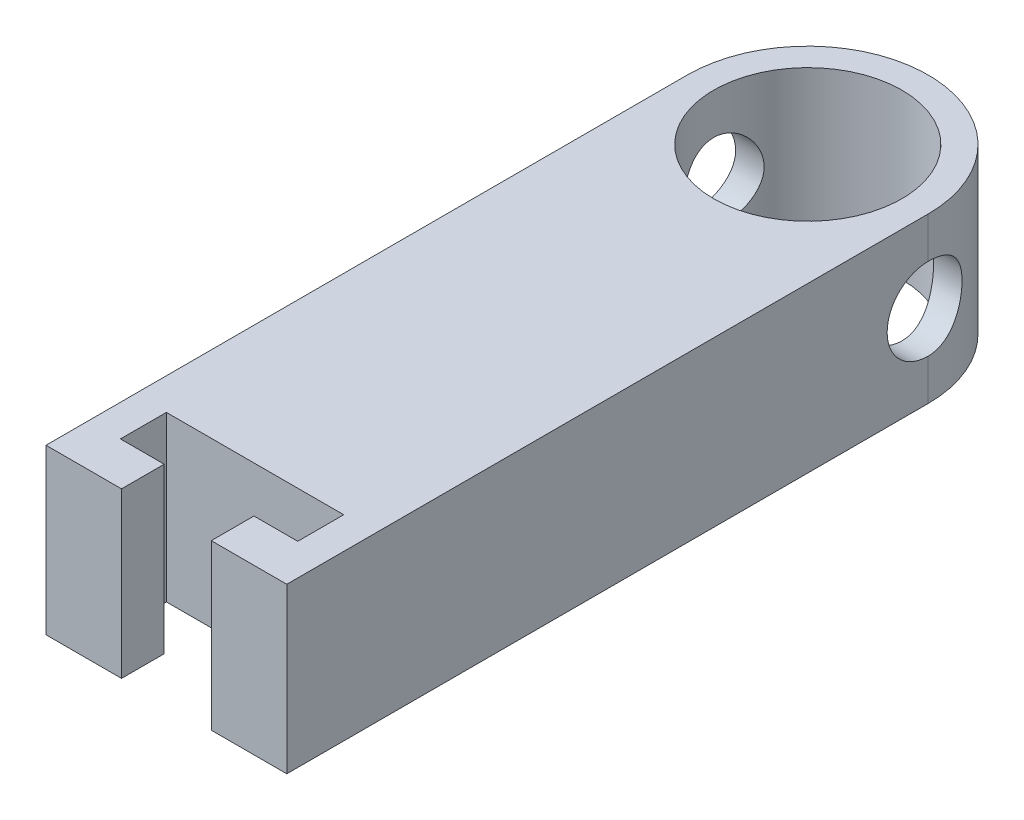
SolidWorks part; units mm, degrees
ref_plane "Front Plane" through (0, 0, 0) normal (0, 0, 1) x (1, 0, 0)
ref_plane "Top Plane" through (0, 0, 0) normal (0, 1, 0) x (1, 0, 0)
ref_plane "Right Plane" through (0, 0, 0) normal (1, 0, 0) x (0, 0, -1)
sketch "Sketch2" plane through (0, 0, 0) normal (0, 0, 1) x (1, 0, 0)
  line L0 (-4.699, 24.13) -> (4.699, 24.13)
  line L1 (-10.16, 20.32) -> (10.16, 20.32)
  line L2 (-10.16, 20.32) -> (-10.16, 27.94)
  line L3 (-10.16, 27.94) -> (10.16, 27.94)
  line L4 (10.16, 20.32) -> (10.16, 27.94)
  line L5 (-10.16, 20.32) -> (10.16, 27.94) construction
  line L6 (-10.16, 27.94) -> (10.16, 20.32) construction
  line L7 (55, 0) -> (-55, 0) construction
  line L8 (-10.16, -27.94) -> (10.16, -20.32) construction
  line L9 (-10.16, -20.32) -> (10.16, -27.94) construction
  line L10 (10.16, -20.32) -> (10.16, -27.94)
  line L11 (-10.16, -27.94) -> (10.16, -27.94)
  line L12 (-10.16, -20.32) -> (-10.16, -27.94)
  line L13 (-10.16, -20.32) -> (10.16, -20.32)
  line L14 (-4.699, -24.13) -> (4.699, -24.13)
  circle A0 centre (4.699, 24.13) radius 1.905
  circle A1 centre (-4.699, 24.13) radius 1.905
  circle A2 centre (-4.699, -24.13) radius 1.905
  circle A3 centre (4.699, -24.13) radius 1.905
  point P0 (0, 24.13)
  point P10 (0, 24.13)
  point P23 (0, -24.13)
  dimension "D5" = 3.81
  dimension "D1" = 20.32
  dimension "D2" = 7.62
  dimension "D3" = 20.32
  dimension "D4" = 9.398
extrude "Boss-Extrude1" add sketch "Sketch2" along normal blind 12.7
sketch "Sketch4" plane through (0, 0, 12.7) normal (0, 0, 1) x (1, 0, 0)
  line L0 (-10.16, -27.94) -> (10.16, -27.94) construction
  line L1 (-10.16, 27.94) -> (-17.78, 27.94)
  line L2 (-10.16, 27.94) -> (-10.16, -27.94)
  line L3 (-10.16, -27.94) -> (-17.78, -27.94)
  line L4 (-17.78, 27.94) -> (-17.78, -27.94)
  dimension "D1" = 7.62
extrude "Boss-Extrude2" add sketch "Sketch4" against normal blind 28.702
sketch "Sketch5" plane through (0, 0, -16.002) normal (0, 0, -1) x (-1, 0, 0)
  line L1 (17.78, 27.94) -> (-10.16, 27.94)
  line L2 (17.78, 27.94) -> (17.78, -27.94)
  line L3 (17.78, -27.94) -> (-10.16, -27.94)
  line L4 (-10.16, 27.94) -> (-10.16, -27.94)
extrude "Boss-Extrude3" add sketch "Sketch5" along normal blind 7.62
sketch "Sketch6" plane through (0, 27.94, 0) normal (0, 1, 0) x (1, 0, 0)
  line L0 (-17.78, 23.622) -> (10.16, 23.622) construction
  line L1 (4.9004, 23.622) -> (10.16, 23.622)
  line L2 (-17.78, 34.544) -> (-17.78, 23.622)
  line L3 (10.16, 34.544) -> (10.16, 23.622)
  line L4 (-17.78, 23.622) -> (-12.5204, 23.622)
  circle A0 centre (-3.81, 34.544) radius 10.922
  arc A1 (-12.5204, 23.622) -> (4.9004, 23.622) centre (-3.81, 34.544) ccw
  circle A2 centre (-3.81, 34.544) radius 13.97 construction
  arc A3 (10.16, 34.544) -> (-17.78, 34.544) centre (-3.81, 34.544) ccw
  point P4 (-3.81, 23.622)
  dimension "D1" = 21.844
  dimension "D2" = 3.048
extrude "Boss-Extrude6" add sketch "Sketch6" against normal up to surface (55.88 mm away) up to face at (-1.905, -27.94, -6.731)
sketch "Sketch7" plane through (10.16, 0, 0) normal (1, 0, 0) x (0, 0, -1)
  line L1 (48.514, 27.94) -> (34.544, 27.94) construction
  circle A0 centre (34.544, 18.415) radius 4.7625
  point P4 (0, 0)
  point P5 (0, 0)
  dimension "D1" = 9.525
  dimension "D2" = 9.525
extrude "Cut-Extrude1" cut sketch "Sketch7" against normal through all both and the other way through all
sketch "Sketch8" plane through (0, 0, -16.002) normal (0, 0, 1) x (1, 0, 0)
  line L1 (-17.78, 27.94) -> (10.16, 27.94)
  line L2 (-17.78, 27.94) -> (-17.78, -27.94)
  line L3 (-17.78, -27.94) -> (10.16, -27.94)
  line L4 (10.16, 27.94) -> (10.16, -27.94)
extrude "Cut-Extrude2" cut sketch "Sketch8" along normal through all
sketch "Sketch9" plane through (0, -27.94, 0) normal (0, -1, 0) x (-1, 0, 0)
  line L3 (-10.16, 16.002) -> (17.78, 16.002)
  line L4 (17.78, 16.002) -> (17.78, 34.544)
  line L5 (-10.16, 34.544) -> (-10.16, 16.002)
  line L6 (-10.16, 16.002) -> (17.78, 16.002)
  line L7 (17.78, 16.002) -> (17.78, 34.544)
  line L8 (-10.16, 34.544) -> (-10.16, 16.002)
  arc A1 (17.78, 34.544) -> (-10.16, 34.544) centre (3.81, 34.544) ccw
  arc A2 (17.78, 34.544) -> (-10.16, 34.544) centre (3.81, 34.544) ccw
  dimension "D1" = 0
extrude "Cut-Extrude3" cut sketch "Sketch9" against normal blind 36.83
sketch "Sketch10" plane through (0, 27.94, 0) normal (0, 1, 0) x (1, 0, 0)
  line L0 (-9.017, -34.671) -> (-9.017, -40.005)
  line L5 (-17.78, 16.002) -> (10.16, 16.002) construction
  line L6 (-13.97, -29.718) -> (6.35, -29.718)
  line L7 (-13.97, -29.718) -> (-13.97, -34.798)
  line L8 (-13.97, -34.798) -> (6.35, -34.798)
  line L9 (6.35, -29.718) -> (6.35, -34.798)
  line L10 (-8.89, -34.798) -> (1.27, -34.798)
  line L11 (-8.89, -34.798) -> (-8.89, -39.878)
  line L12 (-8.89, -39.878) -> (1.27, -39.878)
  line L13 (1.27, -34.798) -> (1.27, -39.878)
  line L14 (10.16, 34.544) -> (10.16, 16.002) construction
  line L15 (-17.78, 16.002) -> (10.16, 16.002)
  line L16 (-17.78, 16.002) -> (-17.78, -39.878)
  line L17 (-17.78, -39.878) -> (10.16, -39.878)
  line L18 (10.16, 16.002) -> (10.16, -39.878)
  line L19 (-3.81, 23.622) -> (10.16, 23.622)
  line L20 (-9.017, -40.005) -> (1.397, -40.005)
  line L21 (1.397, -34.671) -> (1.397, -40.005)
  line L22 (-9.017, -34.671) -> (1.397, -34.671)
  line L23 (-14.097, -29.591) -> (-14.097, -34.925)
  line L24 (-14.097, -34.925) -> (6.477, -34.925)
  line L25 (6.477, -29.591) -> (6.477, -34.925)
  line L26 (-14.097, -29.591) -> (6.477, -29.591)
  circle A0 centre (-3.81, 34.544) radius 10.922 construction
  circle A1 centre (-3.81, 34.544) radius 10.922
  point P4 (-3.81, -29.718)
  point P5 (-3.81, 16.002)
  point P13 (-3.81, -39.878)
  point P25 (-3.81, -8.6885)
  line M17 (-17.78, 16.002) -> (10.16, 16.002)
  dimension "D4" = 53.34
  dimension "D1" = 20.32
  dimension "D2" = 5.08
  dimension "D3" = 10.16
  dimension "D5" = 5.08
  dimension "D6" = 0.127
extrude "Boss-Extrude7" add sketch "Sketch10" against normal up to surface (19.05 mm away) contours L23 L26 L25 L24 L21 L17 L18 L16 L0 M17 up to face at (-3.81, 8.89, -28.7655)
